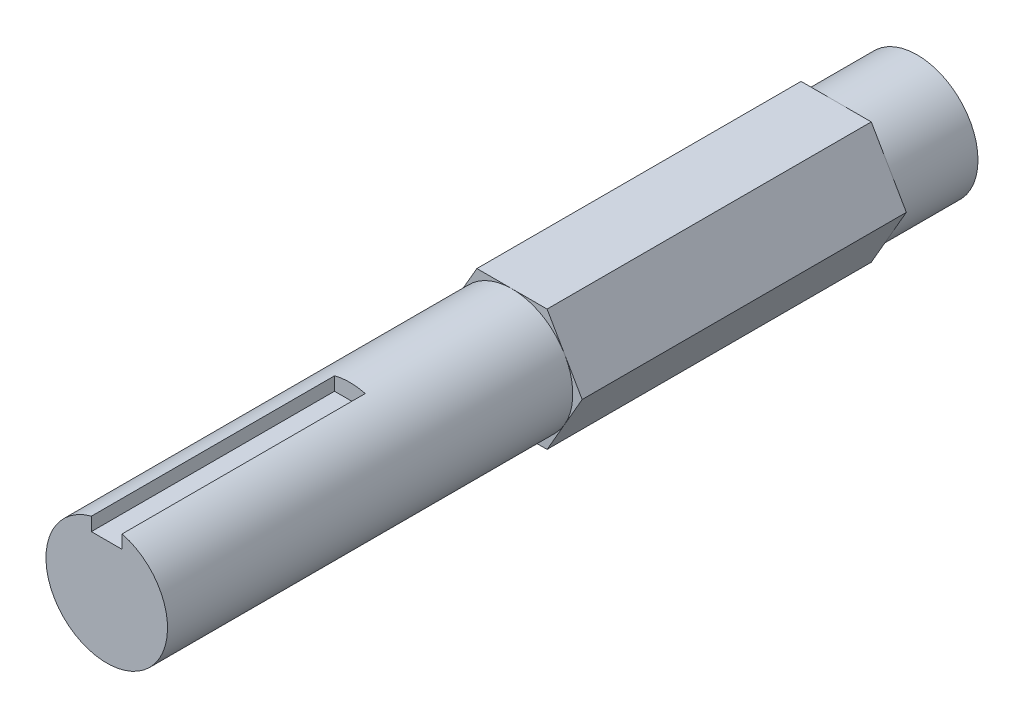
SolidWorks part; units mm, degrees
material "7075-T6 (SN)"
ref_plane "Front Plane" through (0, 0, 0) normal (0, 0, 1) x (1, 0, 0)
ref_plane "Top Plane" through (0, 0, 0) normal (0, 1, 0) x (1, 0, 0)
ref_plane "Right Plane" through (0, 0, 0) normal (1, 0, 0) x (0, 0, -1)
sketch "Sketch1" plane through (0, 0, 0) normal (0, 0, 1) x (1, 0, 0)
  line L1 (-2.7496, -4.7625) -> (2.7496, -4.7625)
  line L2 (2.7496, -4.7625) -> (5.4993, 0)
  line L3 (5.4993, 0) -> (2.7496, 4.7625)
  line L4 (2.7496, 4.7625) -> (-2.7496, 4.7625)
  line L5 (-2.7496, 4.7625) -> (-5.4993, 0)
  line L6 (-5.4993, 0) -> (-2.7496, -4.7625)
  circle A0 centre (0, 0) radius 4.7625 construction
  dimension "D1" = 9.525
extrude "Boss-Extrude1" add sketch "Sketch1" along normal blind 63.5
sketch "Sketch2" plane through (0, 0, 63.5) normal (0, 0, 1) x (1, 0, 0)
  circle A0 centre (0, 0) radius 4.7625
  dimension "D1" = 9.525
extrude "Cut-Extrude1" cut sketch "Sketch2" against normal blind 31.75 flip side to cut
sketch "Sketch3" plane through (0, 0, 0) normal (0, 0, -1) x (-1, 0, 0)
  circle A0 centre (0, 0) radius 4.7625
  dimension "D1" = 9.525
extrude "Cut-Extrude2" cut sketch "Sketch3" against normal blind 6.35 flip side to cut
sketch "Sketch4" plane through (0, 0, 63.5) normal (0, 0, 1) x (1, 0, 0)
  line L0 (2.7496, 4.7625) -> (0, 4.7625) construction
  line L1 (-1.204, 5.9665) -> (1.204, 5.9665)
  line L2 (-1.204, 5.9665) -> (-1.204, 3.5585)
  line L3 (-1.204, 3.5585) -> (1.204, 3.5585)
  line L4 (1.204, 5.9665) -> (1.204, 3.5585)
  line L5 (-1.204, 5.9665) -> (1.204, 3.5585) construction
  line L6 (-1.204, 3.5585) -> (1.204, 5.9665) construction
  circle A0 centre (0, 0) radius 4.7625 construction
  point P0 (0, 4.7625)
  dimension "D1" = 2.4079
extrude "Cut-Extrude3" cut sketch "Sketch4" against normal blind 19.05
